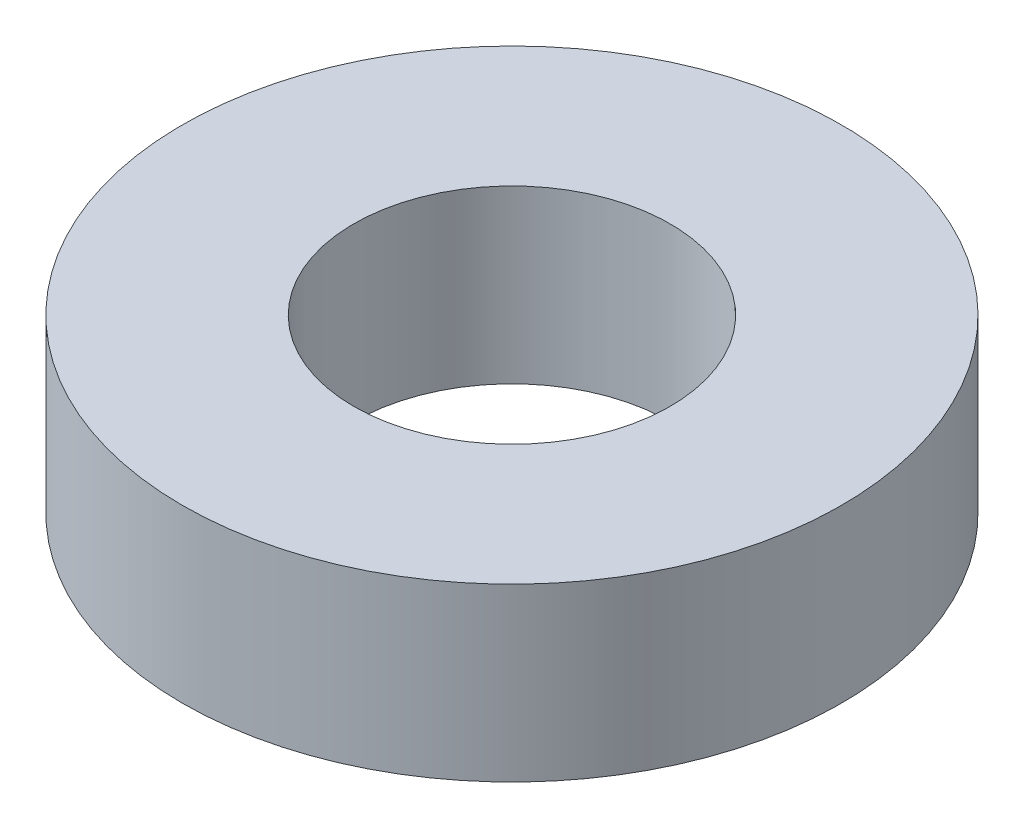
SolidWorks part; units mm, degrees
ref_plane "Front" through (0, 0, 0) normal (0, 0, 1) x (1, 0, 0)
ref_plane "Top" through (0, 0, 0) normal (0, 1, 0) x (1, 0, 0)
ref_plane "Right" through (0, 0, 0) normal (1, 0, 0) x (0, 0, -1)
sketch "Sketch1" plane through (0, 0, 0) normal (0, 1, 0) x (1, 0, 0)
  circle A0 centre (0, 0) radius 2.9308
  circle A1 centre (0, 0) radius 6.1058
  dimension "D1" = 5.8615
  dimension "D2" = 3.175
extrude "Boss-Extrude1" add sketch "Sketch1" along normal blind 3.175
